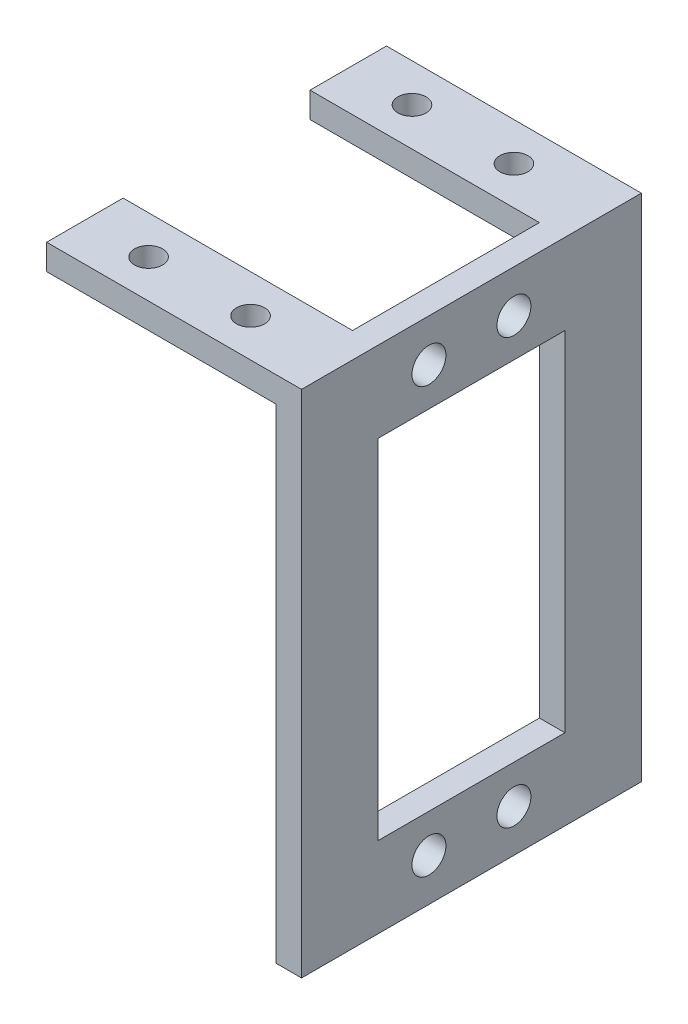
SolidWorks part; units mm, degrees
ref_plane "前视基准面" through (0, 0, 0) normal (0, 0, 1) x (1, 0, 0)
ref_plane "上视基准面" through (0, 0, 0) normal (0, 1, 0) x (1, 0, 0)
ref_plane "右视基准面" through (0, 0, 0) normal (1, 0, 0) x (0, 0, -1)
sketch "草图1" plane through (0, 0, 0) normal (0, 0, 1) x (1, 0, 0)
  line L0 (0, 0) -> (30, 0)
  line L1 (30, 0) -> (30, -60)
  line L2 (0, -3) -> (27, -3)
  line L3 (27, -3) -> (27, -60)
  line L4 (27, -60) -> (30, -60)
  line L5 (0, 0) -> (0, -3)
  dimension "D1" = 30
  dimension "D3" = 60
  dimension "D2" = 3
extrude "凸台-拉伸1" add sketch "草图1" along normal blind 40
sketch "草图2" plane through (0, 0, 0) normal (0, 1, 0) x (1, 0, 0)
  line L0 (0, 0) -> (0, -9) construction
  line L1 (0, -40) -> (0, 0) construction
  line L2 (0, -9) -> (27, -9)
  line L3 (30, -40) -> (30, 0) construction
  line L4 (27, -9) -> (27, 0) construction
  line L5 (27, 0) -> (0, 0) construction
  line L6 (0, -20) -> (30, -20) construction
  line L7 (27, -31) -> (27, -40) construction
  line L8 (0, -31) -> (27, -31)
  line L9 (0, -40) -> (0, -31) construction
  line L10 (27, -40) -> (0, -40) construction
  line L11 (27, -40) -> (27, 0) construction
  line L12 (27, -9) -> (27, -31)
  line L13 (0, -9) -> (0, -31)
  line L14 (7.5, -4.5) -> (19.5, -4.5) construction
  line L15 (13.5, -4.5) -> (13.5, 0) construction
  line L16 (13.5, -4.5) -> (13.5, -9) construction
  line L17 (30, -40) -> (30, 0) construction
  circle A0 centre (7.5, -4.5) radius 1.65
  circle A1 centre (19.5, -4.5) radius 1.65
  circle A2 centre (19.5, -35.5) radius 1.65
  circle A3 centre (7.5, -35.5) radius 1.65
  dimension "D2" = 3.3
  dimension "D3" = 12
  dimension "D1" = 9
extrude "切除-拉伸2" cut sketch "草图2" against normal blind 10
sketch "草图3" plane through (30, 0, 0) normal (1, 0, 0) x (0, 0, -1)
  line L0 (-20, 0) -> (-20, -71.9676) construction
  line L1 (-40, 0) -> (0, 0) construction
  line L2 (-25, -5) -> (-15, -5) construction
  line L3 (-40, -3) -> (-31, -3) construction
  line L4 (-15, -5) -> (-15, -55) construction
  line L5 (-15, -30) -> (-20, -30) construction
  line L7 (-31, -50.5) -> (-9, -50.5)
  line L8 (-31, -50.5) -> (-31, -9.5)
  line L9 (-31, -9.5) -> (-9, -9.5)
  line L10 (-9, -50.5) -> (-9, -9.5)
  line L11 (-31, -50.5) -> (-9, -9.5) construction
  line L12 (-31, -9.5) -> (-9, -50.5) construction
  circle A0 centre (-25, -5) radius 2
  circle A1 centre (-15, -5) radius 2
  circle A2 centre (-15, -55) radius 2
  circle A3 centre (-25, -55) radius 2
  dimension "D3" = 4
  dimension "D4" = 50
  dimension "D1" = 10
  dimension "D2" = 2
  dimension "D5" = 22
  dimension "D6" = 41
extrude "切除-拉伸3" cut sketch "草图3" against normal blind 10
